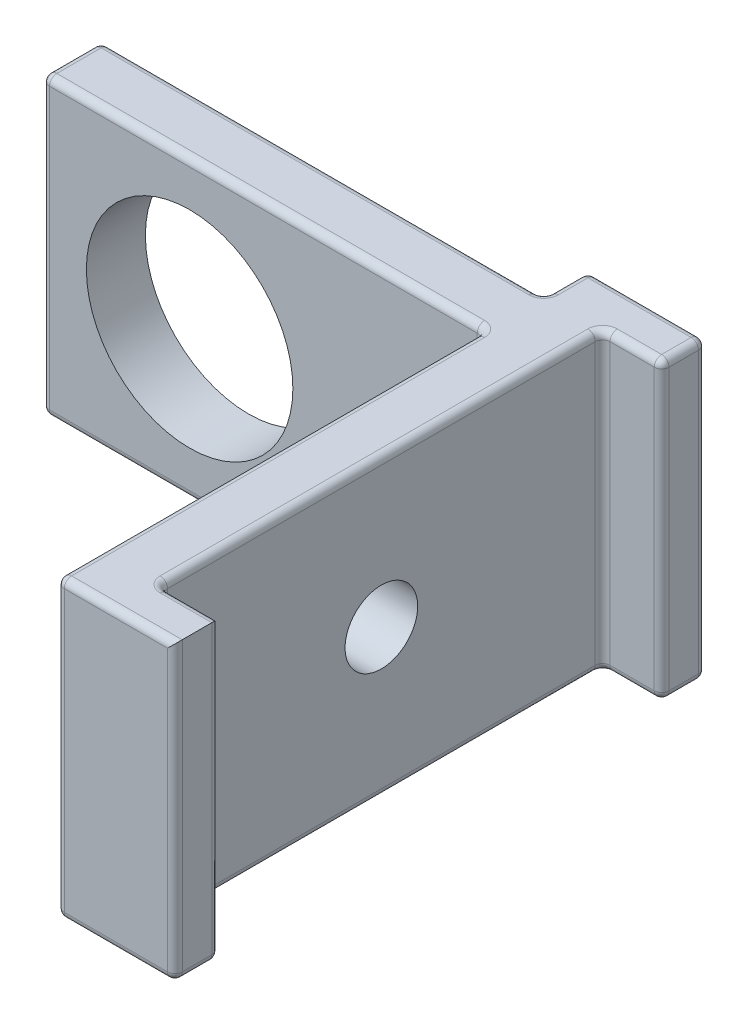
SolidWorks part; units mm, degrees
material "Lega 1060"
ref_plane "Piano frontale" through (0, 0, 0) normal (0, 0, 1) x (1, 0, 0)
ref_plane "Piano superiore" through (0, 0, 0) normal (0, 1, 0) x (1, 0, 0)
ref_plane "Piano destro" through (0, 0, 0) normal (1, 0, 0) x (0, 0, -1)
sketch "Schizzo1" plane through (0, 0, 0) normal (0, 0, 1) x (1, 0, 0)
  line L1 (-10, 10) -> (20, 10)
  line L2 (-10, 10) -> (-10, -10)
  line L3 (-10, -10) -> (20, -10)
  line L4 (20, 10) -> (20, -10)
  circle A1 centre (0, 0) radius 7
  dimension "D1" = 10
  dimension "D5" = 14
  dimension "D2" = 10
  dimension "D3" = 10
  dimension "D4" = 30
extrude "Estrusione-Estrusione1" add sketch "Schizzo1" along normal blind 4
sketch "Schizzo2" plane through (0, 0, 0) normal (0, 0, -1) x (-1, 0, 0)
  line L1 (-20, -10) -> (-24, -10)
  line L2 (-20, -10) -> (-20, 10)
  line L3 (-20, 10) -> (-24, 10)
  line L4 (-24, -10) -> (-24, 10)
extrude "Estrusione-Estrusione2" add sketch "Schizzo2" against normal blind 30
sketch "Schizzo3" plane through (0, 0, 30) normal (0, 0, 1) x (1, 0, 0)
  line L1 (20, -10) -> (28, -10)
  line L2 (20, -10) -> (20, 10)
  line L3 (20, 10) -> (28, 10)
  line L4 (28, -10) -> (28, 10)
extrude "Estrusione-Estrusione3" add sketch "Schizzo3" along normal blind 3
sketch "Schizzo4" plane through (0, 0, 0) normal (0, 0, -1) x (-1, 0, 0)
  line L0 (10, -10) -> (-24, -10) construction
  line L5 (-28, 10) -> (-20, 10)
  line L6 (-28, 10) -> (-28, -10)
  line L7 (-28, -10) -> (-20, -10)
  line L8 (-20, 10) -> (-20, -10)
extrude "Estrusione-Estrusione4" add sketch "Schizzo4" along normal blind 3
fillet "Raccordo1" radius 0.5 4 edges at (20, 0, 4) (20, 0, 0) (24, 0, 0) (24, 0, 30)
fillet "Raccordo2" radius 0.5 7 edges at (4.75, -10, 0) (20, -10, -1.75) (4.75, 10, 0) (19.8536, 10, -0.1464) (19.8536, -10, -0.1464) (28, 0, 0) (20, 10, -1.75)
fillet "Raccordo3" radius 0.5 7 edges at (26.25, -10, 30) (24, -10, 15) (28, -10, -1.75) (27.8536, -10, -0.1464) (24.1464, -10, 29.8536) (24.1464, -10, 0.1464) (26, -10, 0)
fillet "Raccordo4" radius 0.5 10 edges at (28, 0.25, 30) (28, -9.8536, 30.1464) (28, -10, 31.75) (26.25, 10, 30) (24, 10, 15) (28, 10, -1.75) (27.8536, 10, -0.1464) (24.1464, 10, 29.8536) (24.1464, 10, 0.1464) (26, 10, 0)
fillet "Raccordo5" radius 0.5 25 edges at (20.1464, -9.8536, -3) (-10, -9.8536, 0.1464) (19.8536, -10, 4.1464) (24, -10, -3) (20, 0, -3) (24, 10, -3) (20, 0, 33) (24, 10, 33) (23.75, -10, 33) (20, 10, 18.75) (19.8536, 10, 4.1464) (20, -10, 18.75) (-10, 0, 0) (-10, 0, 4) (4.75, -10, 4) (4.75, 10, 4) (20.1464, 9.8536, -3) (-10, 9.8536, 0.1464) (28, 0.25, 33) (27.8536, -9.8536, 33) (-10, -10, 2.25) (-10, 10, 2.25) (27.8536, -9.8536, -3) (28, 0, -3) (27.8536, 9.8536, -3)
sketch "Schizzo5" plane through (24, 0, 0) normal (1, 0, 0) x (0, 0, -1)
  line L0 (-30, 9.5) -> (-30, -9.5) construction
  circle A0 centre (-15, 0) radius 2.4622
  dimension "D1" = 15
extrude "Taglio-Estrusione1" cut sketch "Schizzo5" against normal blind 5
